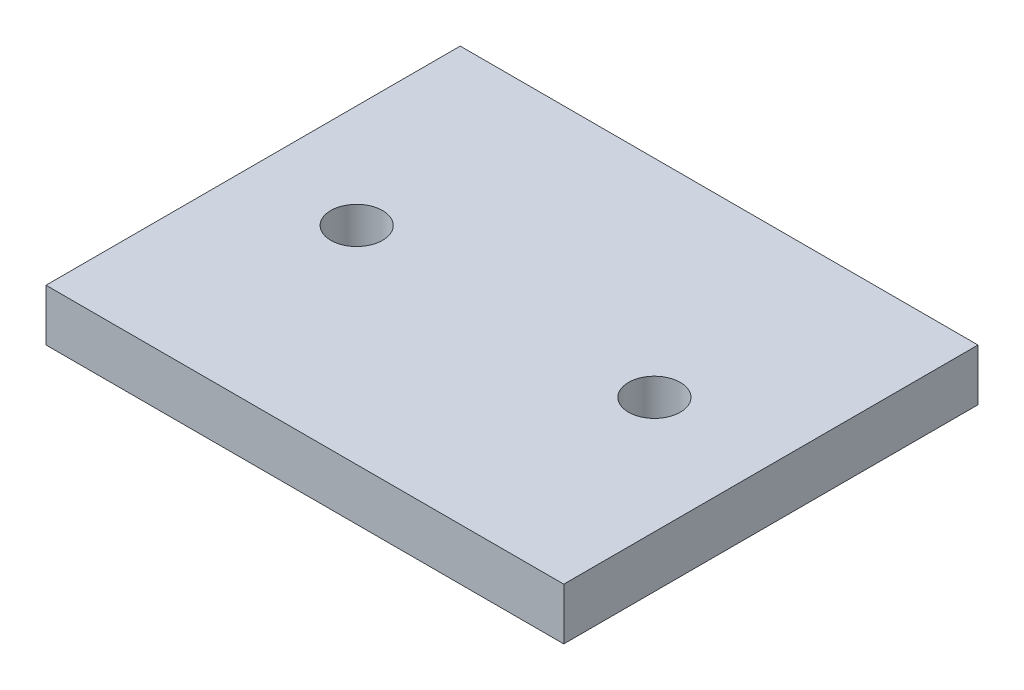
SolidWorks part; units mm, degrees
ref_plane "Front Plane" through (0, 0, 0) normal (0, 0, 1) x (1, 0, 0)
ref_plane "Top Plane" through (0, 0, 0) normal (0, 1, 0) x (1, 0, 0)
ref_plane "Right Plane" through (0, 0, 0) normal (1, 0, 0) x (0, 0, -1)
sketch "Sketch2" plane through (0, 0, 0) normal (0, 1, 0) x (1, 0, 0)
  line L1 (0, 0) -> (127, 0)
  line L2 (0, 0) -> (0, -101.6)
  line L3 (0, -101.6) -> (127, -101.6)
  line L4 (127, 0) -> (127, -101.6)
  circle A0 centre (25.4, -50.8) radius 6.35
  circle A1 centre (98.425, -50.8) radius 6.35
  point P9 (0, 0)
  dimension "D3" = 12.7
  dimension "D4" = 12.7
  dimension "D5" = 50.8
  dimension "D6" = 25.4
  dimension "D7" = 73.025
  dimension "D1" = 101.6
  dimension "D2" = 127
extrude "Boss-Extrude1" add sketch "Sketch2" along normal blind 12.7
